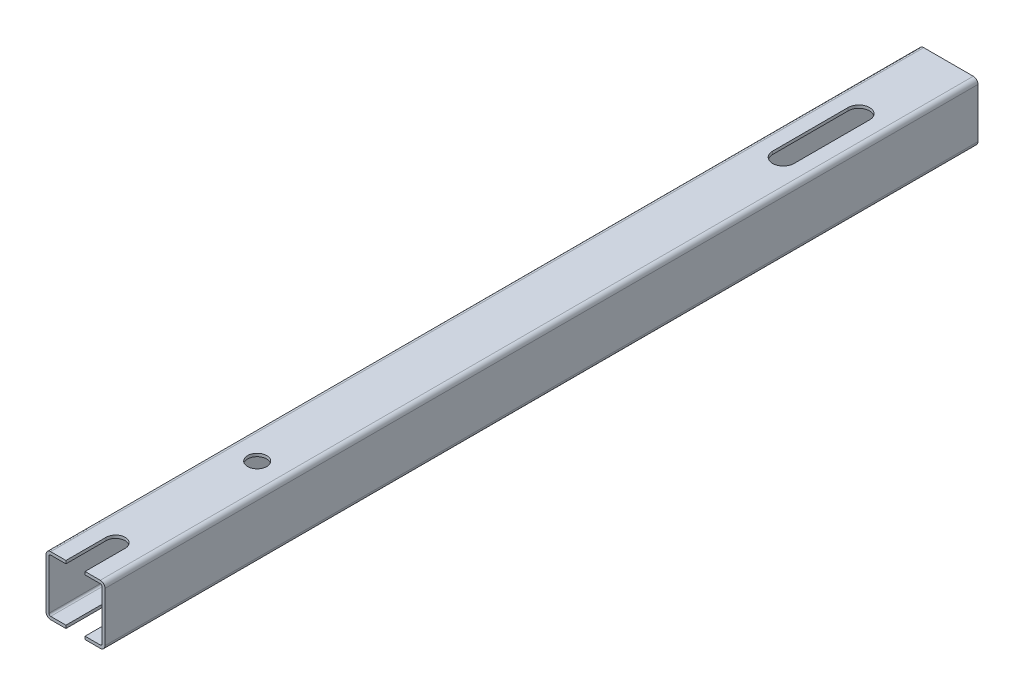
SolidWorks part; units mm, degrees
material "Thornel Mat VMA"
ref_plane "Front Plane" through (0, 0, 0) normal (0, 0, 1) x (1, 0, 0)
ref_plane "Top Plane" through (0, 0, 0) normal (0, 1, 0) x (1, 0, 0)
ref_plane "Right Plane" through (0, 0, 0) normal (1, 0, 0) x (0, 0, -1)
sketch "Sketch1" plane through (0, 0, 0) normal (0, 0, 1) x (1, 0, 0)
  line L0 (2, 1.25) -> (23, 1.25)
  line L1 (2, 0) -> (23, 0)
  line L2 (0, 2) -> (0, 23)
  line L3 (2, 25) -> (23, 25)
  line L4 (25, 2) -> (25, 23)
  line L5 (23.75, 2) -> (23.75, 23)
  line L6 (2, 23.75) -> (23, 23.75)
  line L7 (1.25, 2) -> (1.25, 23)
  arc A0 (23, 0) -> (25, 2) centre (23, 2) ccw
  arc A1 (2, 0) -> (0, 2) centre (2, 2) cw
  arc A2 (23, 25) -> (25, 23) centre (23, 23) cw
  arc A3 (0, 23) -> (2, 25) centre (2, 23) cw
  arc A4 (23, 1.25) -> (23.75, 2) centre (23, 2) ccw
  arc A5 (23, 23.75) -> (23.75, 23) centre (23, 23) cw
  arc A6 (1.25, 23) -> (2, 23.75) centre (2, 23) cw
  arc A7 (2, 1.25) -> (1.25, 2) centre (2, 2) cw
  point P7 (25, 0)
  point P10 (0, 0)
  point P13 (25, 25)
  point P16 (0, 25)
  dimension "D3" = 2
  dimension "D1" = 25
  dimension "D2" = 25
  dimension "D4" = 1.25
extrude "Boss-Extrude1" add sketch "Sketch1" along normal blind 370
sketch "Sketch2" plane through (0, 25, 0) normal (0, 1, 0) x (1, 0, 0)
  line L0 (12.5, -370) -> (12.5, 0) construction
  line L1 (23, -370) -> (2, -370) construction
  line L2 (23, 0) -> (2, 0) construction
  line L3 (8.45, -353) -> (8.45, -370)
  line L4 (16.55, -353) -> (16.55, -370)
  line L5 (16.55, -370) -> (8.45, -370)
  circle A0 centre (12.5, -293) radius 4.05
  circle A1 centre (12.5, -353) radius 4.05 construction
  arc A2 (8.45, -353) -> (16.55, -353) centre (12.5, -353) cw
  dimension "D2" = 8.1
  dimension "D1" = 60
  dimension "D3" = 17
extrude "Cut-Extrude1" cut sketch "Sketch2" against normal through all
sketch "Sketch3" plane through (0, 25, 0) normal (0, 1, 0) x (1, 0, 0)
  line L0 (12.5, 0) -> (12.5, -150.2098) construction
  line L1 (23, 0) -> (2, 0) construction
  line L2 (12.5, -38) -> (12.5, -70) construction
  line L3 (17.05, -38) -> (17.05, -70)
  line L4 (7.95, -38) -> (7.95, -70)
  arc A0 (17.05, -38) -> (7.95, -38) centre (12.5, -38) ccw
  arc A1 (7.95, -70) -> (17.05, -70) centre (12.5, -70) ccw
  point P6 (12.5, -54)
  dimension "D1" = 9.1
  dimension "D2" = 32
  dimension "D3" = 38
extrude "Cut-Extrude2" cut sketch "Sketch3" against normal up to next
sketch "Sketch4" plane through (0, 0, 0) normal (0, -1, 0) x (1, 0, 0)
  line L0 (12.5, 0) -> (12.5, 76.7979) construction
  line L1 (2, 0) -> (23, 0) construction
  line L2 (7.95, 0) -> (7.95, 17)
  line L3 (17.05, 17) -> (17.05, 0)
  line L4 (17.05, 0) -> (7.95, 0)
  arc A0 (7.95, 17) -> (17.05, 17) centre (12.5, 17) cw
  circle A1 centre (12.5, 53) radius 6
  dimension "D4" = 12
  dimension "D1" = 9.1
  dimension "D2" = 17
  dimension "D3" = 53
extrude "Cut-Extrude3" cut sketch "Sketch4" against normal up to next
